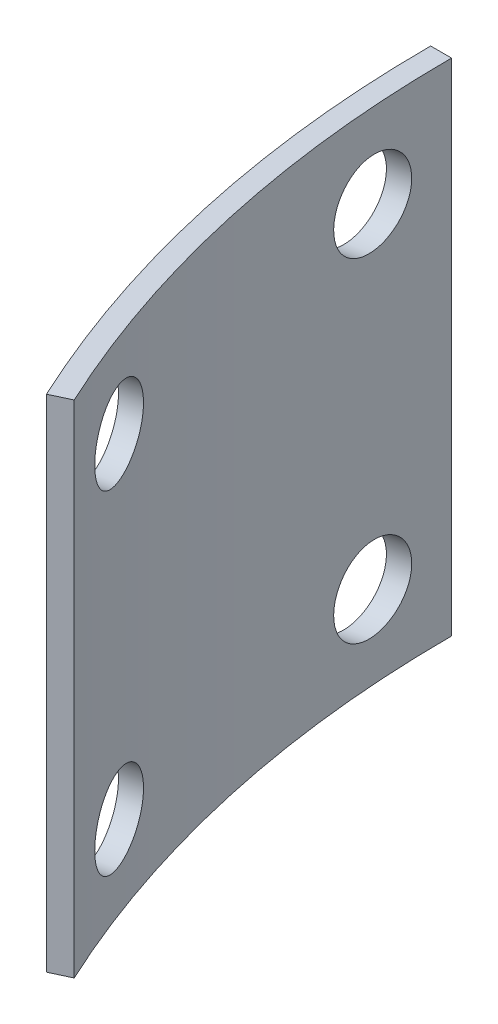
SolidWorks part; units mm, degrees
material "Carbon Fiber (2)"
ref_plane "Front Plane" through (0, 0, 0) normal (0, 0, 1) x (1, 0, 0)
ref_plane "Top Plane" through (0, 0, 0) normal (0, 1, 0) x (1, 0, 0)
ref_plane "Right Plane" through (0, 0, 0) normal (1, 0, 0) x (0, 0, -1)
sketch "Sketch2" plane through (0, 0, 0) normal (0, 1, 0) x (1, 0, 0)
  line L0 (0, 0) -> (-88.9, 0)
  line L1 (-80.5708, -37.5708) -> (0, 0)
  arc A1 (-88.9, 0) -> (-80.5708, -37.5708) centre (0, 0) ccw
  arc A2 (-87.3125, 0) -> (-79.132, -36.8999) centre (0, 0) ccw
  point P6 (0, 0)
  dimension "D1" = 88.9
  dimension "D3" = 1.5875
  dimension "D2" = 25
extrude "Boss-Extrude1" add sketch "Sketch2" along normal blind 38.1 contours A2 L0 A1 L1
ref_plane "Plane1" through (-86.7927, 0, 19.2415) normal (-0.9763, 0, 0.2164) x (0, -1, 0)
sketch "Sketch3" plane through (-86.7927, 0, 19.2415) normal (-0.9763, 0, 0.2164) x (0, -1, 0)
  line L0 (0, 0) -> (-38.1, 0) construction
  line L1 (-31.75, 0) -> (-31.75, -12.7) construction
  line L2 (-31.75, 0) -> (-31.75, 12.7) construction
  line L3 (-6.35, 0) -> (-6.35, -12.7) construction
  line L4 (-6.35, 0) -> (-6.35, 12.7) construction
  circle A0 centre (-31.75, -12.7) radius 3.175
  circle A1 centre (-31.75, 12.7) radius 3.175
  circle A2 centre (-6.35, -12.7) radius 3.175
  circle A3 centre (-6.35, 12.7) radius 3.175
  dimension "D5" = 6.35
  dimension "D1" = 38.1
  dimension "D2" = 12.7
  dimension "D3" = 6.35
  dimension "D4" = 6.35
extrude "Cut-Extrude1" cut sketch "Sketch3" against normal blind 38.1
